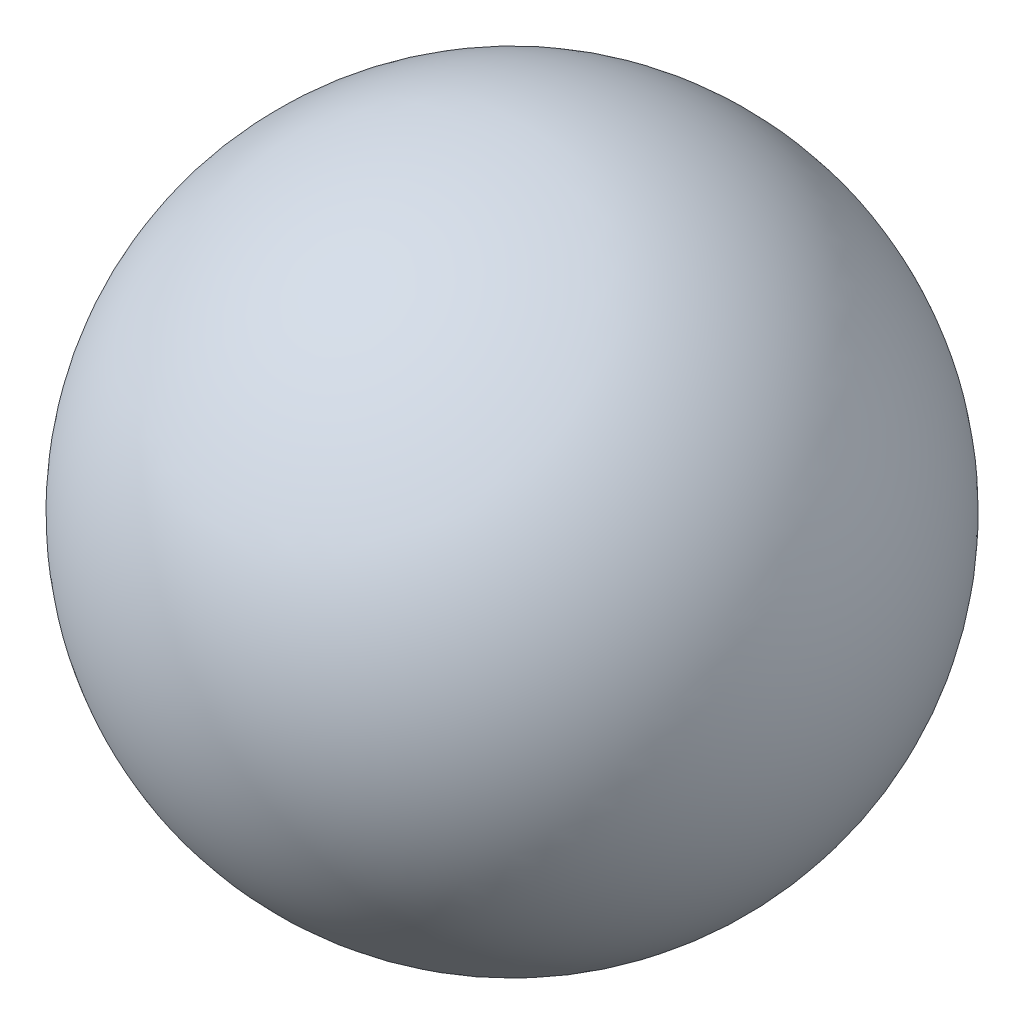
SolidWorks part; units mm, degrees
material "Ti-5Al-2.5Sn Annealed (SS)"
ref_plane "Front Plane" through (0, 0, 0) normal (0, 0, 1) x (1, 0, 0)
ref_plane "Top Plane" through (0, 0, 0) normal (0, 1, 0) x (1, 0, 0)
ref_plane "Right Plane" through (0, 0, 0) normal (1, 0, 0) x (0, 0, -1)
sketch "Sketch2" plane through (0, 0, 0) normal (0, 1, 0) x (1, 0, 0)
  line L0 (0, -1.5875) -> (0, 1.5875)
  arc A0 (0, -1.5875) -> (0, 1.5875) centre (0, 0) ccw
revolve "Revolve3" add sketch "Sketch2" angle 360 about L0
